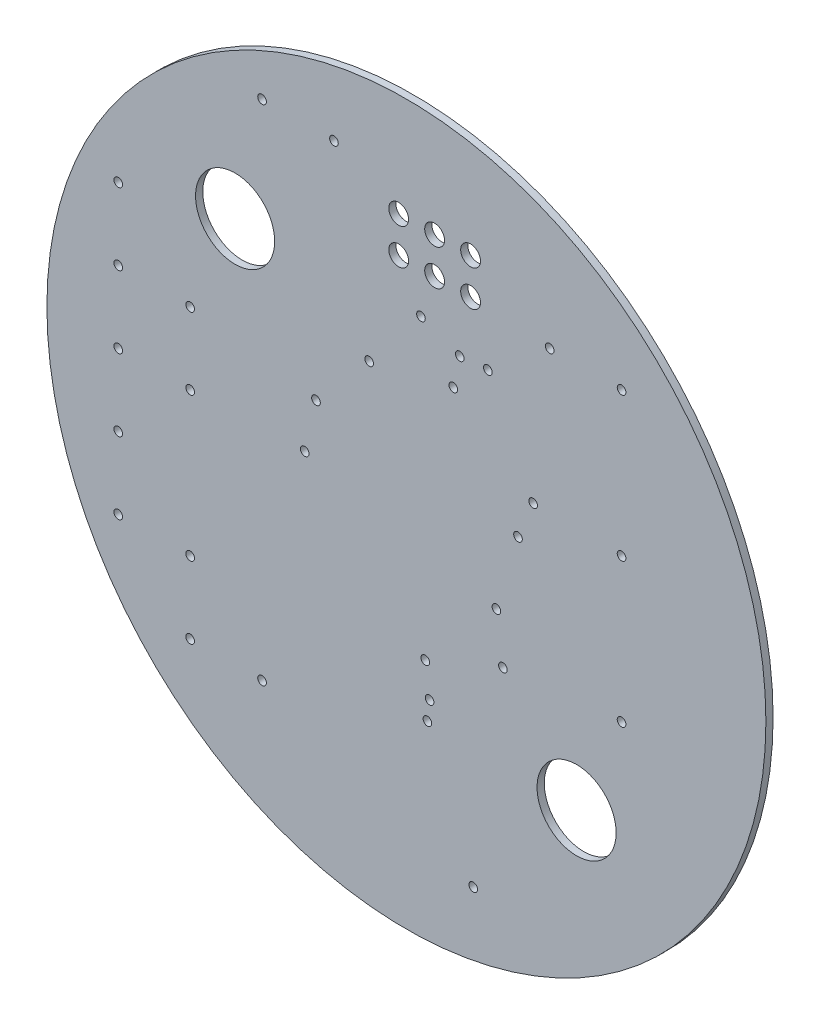
SolidWorks part; units mm, degrees
ref_plane "Front Plane" through (0, 0, 0) normal (0, 0, 1) x (1, 0, 0)
ref_plane "Top Plane" through (0, 0, 0) normal (0, 1, 0) x (1, 0, 0)
ref_plane "Right Plane" through (0, 0, 0) normal (1, 0, 0) x (0, 0, -1)
ref_plane "Conductive_Layer Bottom" through (0, 0, 0.034) normal (0, 0, 1) x (1, 0, 0)
ref_plane "Dielectric_Layer Bottom" through (0, 0, 0.288) normal (0, 0, 1) x (1, 0, 0)
ref_plane "Conductive_Layer Top" through (0, 0, 0.322) normal (0, 0, 1) x (1, 0, 0)
sketch "Sketch1" plane through (0, 0, 0) normal (0, 0, 1) x (1, 0, 0)
  arc A0 (-8.961, -8.961) -> (9, 9) centre (0.0195, 0.0195) ccw
  arc A1 (9, 9) -> (-8.961, -8.961) centre (0.0195, 0.0195) ccw
extrude "Board_Outline" add sketch "Sketch1" along normal blind 0.254 from offset 0.034 separate body
imported_body "Bottom"
imported_body "Top"
sketch "Sketch2" plane through (0, 0, 0) normal (0, 0, 1) x (1, 0, 0)
  circle A0 centre (-1.295, 4.039) radius 0.1525
  circle A1 centre (-3.572, 0.144) radius 0.1525
  circle A2 centre (0.533, 6.325) radius 0.1525
  circle A3 centre (2.896, 5.867) radius 0.1525
  circle A4 centre (1.676, 4.724) radius 0.1525
  circle A5 centre (0.686, -4.115) radius 0.1525
  circle A6 centre (0.838, -5.258) radius 0.1525
  circle A7 centre (0.762, -5.944) radius 0.1525
  circle A8 centre (3.2, -1.295) radius 0.1525
  circle A9 centre (4.496, 2.591) radius 0.1525
  circle A10 centre (3.962, 1.295) radius 0.1525
  circle A11 centre (2.381, -10.211) radius 0.1525
  circle A12 centre (3.429, -2.972) radius 0.1525
  circle A13 centre (1.905, 5.791) radius 0.1525
  circle A14 centre (-3.175, 1.905) radius 0.1525
extrude "Via" cut sketch "Sketch2" along normal through all
sketch "Sketch3" plane through (0, 0, 0) normal (0, 0, 1) x (1, 0, 0)
  circle A0 centre (6.032, -6.032) radius 1.397
  circle A1 centre (-6.032, 6.032) radius 1.397
extrude "NPTH" cut sketch "Sketch3" along normal through all
sketch "Sketch4" plane through (0, 0, 0) normal (0, 0, 1) x (1, 0, 0)
  circle A0 centre (2.286, 9.068) radius 0.35
  circle A1 centre (1.016, 9.068) radius 0.35
  circle A2 centre (-0.254, 9.068) radius 0.35
  circle A3 centre (2.286, 7.798) radius 0.35
  circle A4 centre (1.016, 7.798) radius 0.35
  circle A5 centre (-0.254, 7.798) radius 0.35
  circle A6 centre (-7.62, 2.54) radius 0.1525
  circle A7 centre (-7.62, 0) radius 0.1525
  circle A8 centre (-10.16, 5.08) radius 0.1525
  circle A9 centre (7.62, -2.54) radius 0.1525
  circle A10 centre (5.08, 7.62) radius 0.1525
  circle A11 centre (-7.62, -7.62) radius 0.1525
  circle A12 centre (-5.08, -7.62) radius 0.1525
  circle A13 centre (-7.62, -5.08) radius 0.1525
  circle A14 centre (-10.16, -2.54) radius 0.1525
  circle A15 centre (-10.16, 0) radius 0.1525
  circle A16 centre (-10.16, 2.54) radius 0.1525
  circle A17 centre (7.62, 2.54) radius 0.1525
  circle A18 centre (7.62, 7.62) radius 0.1525
  circle A19 centre (-10.16, -5.08) radius 0.1525
  circle A20 centre (-5.08, 10.16) radius 0.1525
  circle A21 centre (-2.54, 10.16) radius 0.1525
extrude "PTH" cut sketch "Sketch4" along normal through all
